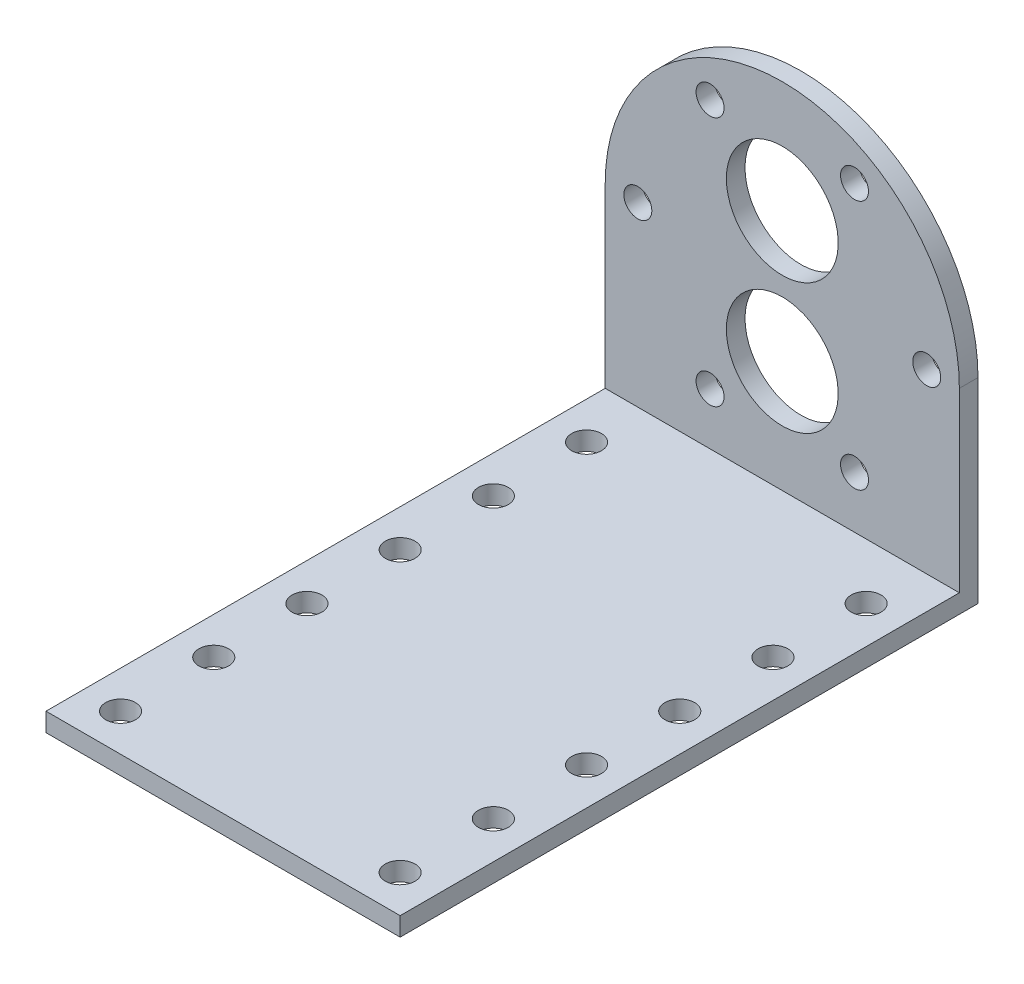
SolidWorks part; units mm, degrees
material "5052-H38"
ref_plane "正面" through (0, 0, 0) normal (0, 0, 1) x (1, 0, 0)
ref_plane "平面" through (0, 0, 0) normal (0, 1, 0) x (1, 0, 0)
ref_plane "右側面" through (0, 0, 0) normal (1, 0, 0) x (0, 0, -1)
sketch "ｽｹｯﾁ1" plane through (0, 0, 0) normal (0, 0, 1) x (1, 0, 0)
  line L0 (-19, 0) -> (-19, -21)
  line L1 (-19, -21) -> (19, -21)
  line L2 (19, -21) -> (19, 0)
  arc A0 (19, 0) -> (-19, 0) centre (0, 0) ccw
  dimension "D1" = 38
  dimension "D2" = 21
extrude "ﾎﾞｽ - 押し出し1" add sketch "ｽｹｯﾁ1" along normal blind 2
sketch "ｽｹｯﾁ2" plane through (0, 0, 2) normal (0, 0, 1) x (1, 0, 0)
  line L0 (19, -21) -> (19, 0) construction
  line L1 (-19, -21) -> (19, -21)
  line L2 (-19, -21) -> (-19, -19)
  line L3 (-19, -19) -> (19, -19)
  line L4 (19, -21) -> (19, -19)
  dimension "D1" = 2
extrude "ﾎﾞｽ - 押し出し2" add sketch "ｽｹｯﾁ2" along normal blind 60
sketch "ｽｹｯﾁ3" plane through (0, -19, 0) normal (0, 1, 0) x (1, 0, 0)
  line L0 (-27.3249, -8) -> (29.2674, -8) construction
  line L1 (-15, 27.7073) -> (-15, -20.3114) construction
  line L2 (15, 21.5385) -> (15, -26.4803) construction
  line L3 (-40.4672, -28) -> (16.1251, -28) construction
  line L4 (-28.9342, -18) -> (27.6581, -18) construction
  line L5 (-28.2637, -38) -> (28.3286, -38) construction
  line L6 (-32.4209, -58) -> (24.1714, -58) construction
  line L7 (-31.214, -48) -> (25.3783, -48) construction
  line L8 (-19, -62) -> (-19, -2) construction
  line L10 (19, 0) -> (-19, 0) construction
  circle A0 centre (-15, -8) radius 1.6
  circle A1 centre (-15, -18) radius 1.6
  circle A2 centre (-15, -38) radius 1.6
  circle A3 centre (-15, -28) radius 1.6
  circle A4 centre (-15, -48) radius 1.6
  circle A5 centre (15, -8) radius 1.6
  circle A6 centre (15, -18) radius 1.6
  circle A7 centre (15, -28) radius 1.6
  circle A8 centre (15, -38) radius 1.6
  circle A9 centre (15, -48) radius 1.6
  circle A10 centre (-15, -58) radius 1.6
  circle A11 centre (15, -58) radius 1.6
  dimension "D9" = 3.2
  dimension "D1" = 30
  dimension "D2" = 4
  dimension "D3" = 8
  dimension "D4" = 10
  dimension "D5" = 10
  dimension "D6" = 10
  dimension "D7" = 10
  dimension "D8" = 10
extrude "ｶｯﾄ - 押し出し1" cut sketch "ｽｹｯﾁ3" against normal blind 2
sketch "ｽｹｯﾁ4" plane through (0, 0, 0) normal (0, 0, -1) x (-1, 0, 0)
  line L0 (0, -16.1936) -> (0, -71.8669) construction
  line L1 (19, -21) -> (-19, -21) construction
  line L3 (-19, -21) -> (-19, 0) construction
  line L5 (0, 0) -> (-45.5658, 0) construction
  circle A0 centre (0, 7) radius 6
  circle A1 centre (0, -7) radius 6
  circle A2 centre (0, 0) radius 18.5
  circle A3 centre (0, 0) radius 15.5 construction
  circle A4 centre (-7.75, 13.4234) radius 1.5
  circle A5 centre (-15.5, 0) radius 1.5
  circle A6 centre (15.5, 0) radius 1.5
  circle A7 centre (7.75, 13.4234) radius 1.5
  circle A8 centre (7.75, -13.4234) radius 1.5
  circle A9 centre (-7.75, -13.4234) radius 1.5
  point P9 (-15.5, 0)
  point P10 (7.75, 13.4234)
  point P16 (7.75, -13.4234)
  point P18 (15.5, 0)
  point P19 (-7.75, 13.4234)
  point P21 (-7.75, -13.4234)
  dimension "D2" = 12
  dimension "D5" = 37
  dimension "D4" = 31
  dimension "D12" = 3
  dimension "D1" = 28
  dimension "D3" = 14
  dimension "D6" = 19
  dimension "D7" = 7
  dimension "D8" = 120
  dimension "D9" = 120
  dimension "D10" = 120
  dimension "D11" = 120
extrude "ｶｯﾄ - 押し出し3" cut sketch "ｽｹｯﾁ4" against normal blind 2 contours A1 | A0 | A7 | A6 | A8 | A5 | A4 | A9
